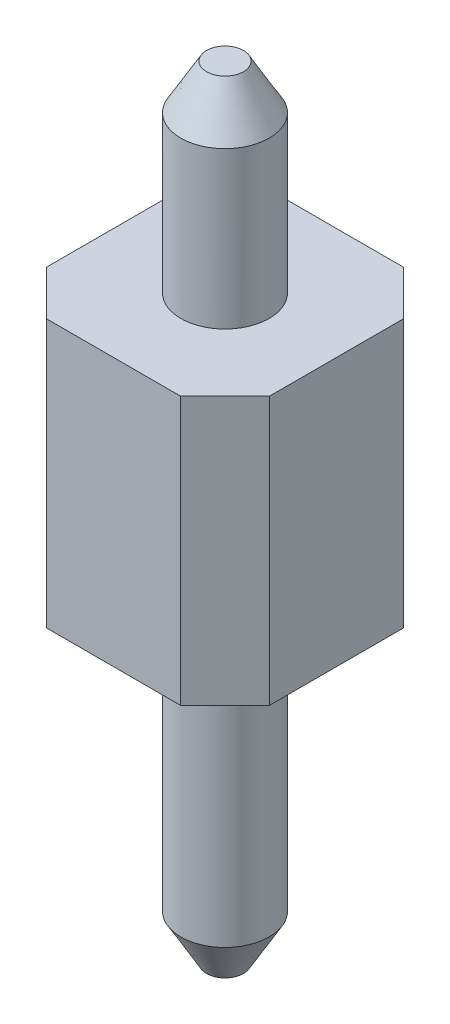
SolidWorks part; units mm, degrees
ref_plane "Front Plane" through (0, 0, 0) normal (0, 0, 1) x (1, 0, 0)
ref_plane "Top Plane" through (0, 0, 0) normal (0, 1, 0) x (1, 0, 0)
ref_plane "Right Plane" through (0, 0, 0) normal (1, 0, 0) x (0, 0, -1)
sketch "Sketch1" plane through (0, 0, 0) normal (0, 1, 0) x (1, 0, 0)
  line L0 (0, 0) -> (0, 69.6893) construction
  line L1 (0, 0) -> (68.5311, 0) construction
  line L2 (-1.25, 1.25) -> (1.25, 1.25)
  line L3 (1.25, 1.25) -> (1.25, -1.25)
  line L4 (-1.25, 1.25) -> (-1.25, -1.25)
  line L5 (-1.25, -1.25) -> (1.25, -1.25)
  point P8 (0, 1.25)
  point P10 (-1.25, 0)
  point P11 (1.25, 0)
  dimension "D1" = 2.5
extrude "Boss-Extrude1" add sketch "Sketch1" along normal mid plane 3
sketch "Sketch2" plane through (0, 1.5, 0) normal (0, 1, 0) x (1, 0, 0)
  line L0 (0, 1.25) -> (0, -1.25) construction
  line L1 (1.25, 0) -> (-1.25, 0) construction
  line L4 (-1.25, -1.25) -> (1.25, -1.25)
  line L5 (1.25, -1.25) -> (1.25, 1.25)
  line L6 (1.25, 1.25) -> (-1.25, 1.25)
  line L7 (-1.25, 1.25) -> (-1.25, -1.25)
  line L8 (-1.25, -1.25) -> (1.25, -1.25)
  line L9 (1.25, -1.25) -> (1.25, 1.25)
  line L10 (1.25, 1.25) -> (-1.25, 1.25)
  line L11 (-1.25, 1.25) -> (-1.25, -1.25)
  circle A0 centre (0, 0) radius 0.4953
  dimension "D2" = 0.9906
  dimension "D1" = 0
extrude "Boss-Extrude2" add sketch "Sketch2" along normal blind 2.25 contours A0
chamfer "Chamfer1" distance 0.5 angle 30 1 edges at (0, 3.75, 0.4953)
chamfer "Chamfer2" distance 0.5 angle 45 4 edges at (-1.25, 0, -1.25) (1.25, 0, -1.25) (1.25, 0, 1.25) (-1.25, 0, 1.25)
sketch "Sketch4" plane through (0, -1.5, 0) normal (0, -1, 0) x (1, 0, 0)
  line L0 (0, 1.25) -> (0, -1.25) construction
  line L1 (-0.75, 1.25) -> (0.75, 1.25) construction
  line L2 (0.75, -1.25) -> (-0.75, -1.25) construction
  line L3 (1.25, 0) -> (-1.25, 0) construction
  line L4 (1.25, 0.75) -> (1.25, -0.75) construction
  line L5 (-1.25, -0.75) -> (-1.25, 0.75) construction
  circle A0 centre (0, 0) radius 0.4953
  dimension "D1" = 0.9906
extrude "Boss-Extrude3" add sketch "Sketch4" along normal blind 3.5
chamfer "Chamfer3" distance 0.5 angle 30 1 edges at (0, -5, -0.4953)
